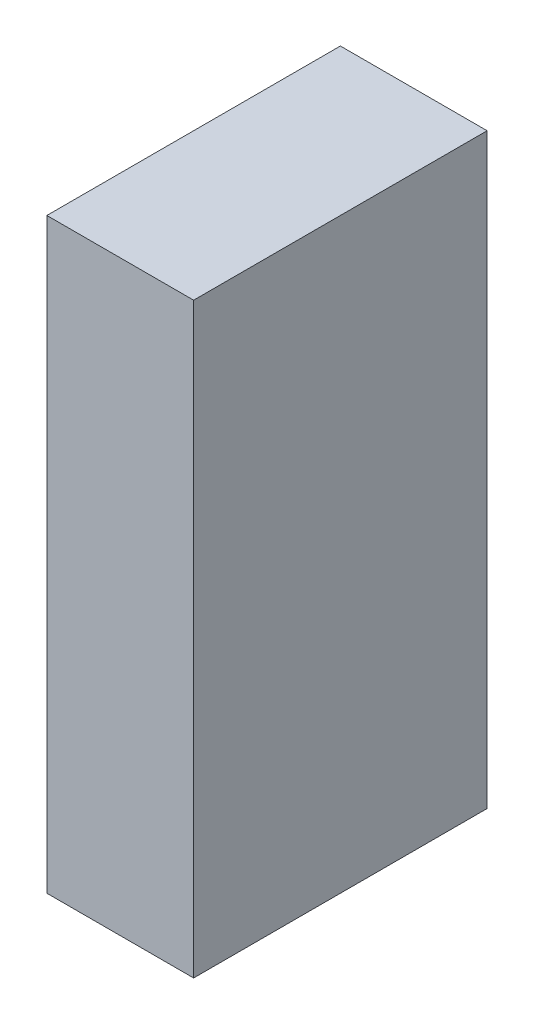
SolidWorks part; units mm, degrees
material "6061-T6 (SS)"
ref_plane "Front Plane" through (0, 0, 0) normal (0, 0, 1) x (1, 0, 0)
ref_plane "Top Plane" through (0, 0, 0) normal (0, 1, 0) x (1, 0, 0)
ref_plane "Right Plane" through (0, 0, 0) normal (1, 0, 0) x (0, 0, -1)
sketch "Sketch1" plane through (0, 0, 0) normal (0, 1, 0) x (1, 0, 0)
  line L1 (-12.7, 25.4) -> (12.7, 25.4)
  line L2 (-12.7, 25.4) -> (-12.7, -25.4)
  line L3 (-12.7, -25.4) -> (12.7, -25.4)
  line L4 (12.7, 25.4) -> (12.7, -25.4)
  line L5 (-12.7, 25.4) -> (12.7, -25.4) construction
  line L6 (-12.7, -25.4) -> (12.7, 25.4) construction
  point P0 (0, 0)
  dimension "D1" = 50.8
  dimension "D2" = 25.4
extrude "Boss-Extrude1" add sketch "Sketch1" along normal blind 101.6
